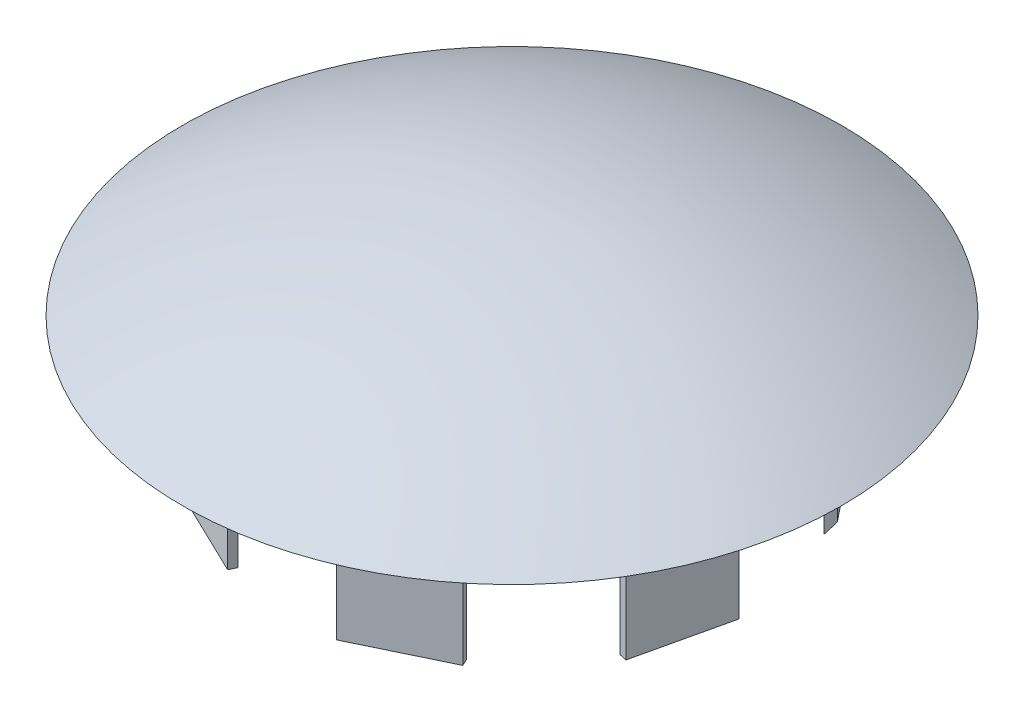
SolidWorks part; units mm, degrees
material "Custom Plastic PLA"
ref_plane "Front Plane" through (0, 0, 0) normal (0, 0, 1) x (1, 0, 0)
ref_plane "Top Plane" through (0, 0, 0) normal (0, 1, 0) x (1, 0, 0)
ref_plane "Right Plane" through (0, 0, 0) normal (1, 0, 0) x (0, 0, -1)
sketch "Sketch1" plane through (0, 0, 0) normal (0, 1, 0) x (1, 0, 0)
  line L6 (7.3408, 107.3746) -> (-14.4622, 96.8748)
  line L7 (-14.4622, 96.8748) -> (-29.5503, 77.9549)
  line L8 (-29.5503, 77.9549) -> (-34.9352, 54.3622)
  line L9 (-34.9352, 54.3622) -> (-29.5503, 30.7694)
  line L10 (-29.5503, 30.7694) -> (-14.4622, 11.8495)
  line L11 (-14.4622, 11.8495) -> (7.3408, 1.3497)
  line L12 (7.3408, 1.3497) -> (31.5403, 1.3497)
  line L13 (31.5403, 1.3497) -> (53.3433, 11.8495)
  line L14 (53.3433, 11.8495) -> (68.4314, 30.7694)
  line L15 (68.4314, 30.7694) -> (73.8163, 54.3622)
  line L16 (73.8163, 54.3622) -> (68.4314, 77.9549)
  line L17 (68.4314, 77.9549) -> (53.3433, 96.8748)
  line L18 (53.3433, 96.8748) -> (31.5403, 107.3746)
  line L31 (4.0802, 52.7357) -> (31.0802, 52.7357)
  line L32 (4.0802, 52.7357) -> (4.0802, 39.7357)
  line L33 (4.0802, 39.7357) -> (31.0802, 39.7357)
  line L34 (31.0802, 52.7357) -> (31.0802, 39.7357)
  line L35 (4.0802, 52.7357) -> (31.0802, 39.7357) construction
  line L36 (4.0802, 39.7357) -> (31.0802, 52.7357) construction
  line L61 (7.3408, 107.3746) -> (31.5403, 107.3746)
  line L62 (7.3408, 107.3746) -> (7.3408, 105.3746)
  line L63 (31.5403, 107.3746) -> (31.5403, 105.3746) construction
  line L65 (7.3408, 105.3746) -> (31.5403, 105.3746)
  line L66 (7.3408, 105.3746) -> (7.3408, 103.3746)
  line L67 (31.5403, 105.3746) -> (31.5403, 103.3746)
  line L68 (7.3408, 103.3746) -> (31.5403, 103.3746)
  line L69 (58.9964, 92.3606) -> (57.4327, 91.1136)
  line L70 (74.0845, 73.4407) -> (72.5208, 72.1937) construction
  line L71 (57.4327, 91.1136) -> (72.5208, 72.1937)
  line L72 (57.4327, 91.1136) -> (55.869, 89.8666)
  line L73 (55.869, 89.8666) -> (70.9572, 70.9467)
  line L74 (72.5208, 72.1937) -> (70.9572, 70.9467)
  line L75 (79.4647, 42.6136) -> (77.5148, 43.0587)
  line L76 (74.0798, 19.0209) -> (72.1299, 19.4659) construction
  line L77 (77.5148, 43.0587) -> (72.1299, 19.4659)
  line L78 (77.5148, 43.0587) -> (75.565, 43.5037)
  line L79 (75.565, 43.5037) -> (70.1801, 19.911)
  line L80 (72.1299, 19.4659) -> (70.1801, 19.911)
  line L81 (53.3327, -4.4059) -> (52.465, -2.6039)
  line L82 (31.5297, -14.9056) -> (30.662, -13.1037) construction
  line L83 (52.465, -2.6039) -> (30.662, -13.1037)
  line L84 (52.465, -2.6039) -> (51.5972, -0.802)
  line L85 (51.5972, -0.802) -> (29.7942, -11.3018)
  line L86 (30.662, -13.1037) -> (29.7942, -11.3018)
  line L87 (0.2784, -13.2913) -> (1.1461, -11.4893)
  line L88 (-21.5246, -2.7915) -> (-20.6568, -0.9896) construction
  line L89 (1.1461, -11.4893) -> (-20.6568, -0.9896)
  line L90 (1.1461, -11.4893) -> (2.0139, -9.6874)
  line L91 (2.0139, -9.6874) -> (-19.7891, 0.8123)
  line L92 (-20.6568, -0.9896) -> (-19.7891, 0.8123)
  line L93 (-39.7474, 22.6483) -> (-37.7975, 23.0934)
  line L94 (-45.1322, 46.2411) -> (-43.1824, 46.6861) construction
  line L95 (-37.7975, 23.0934) -> (-43.1824, 46.6861)
  line L96 (-37.7975, 23.0934) -> (-35.8476, 23.5384)
  line L97 (-35.8476, 23.5384) -> (-41.2325, 47.1311)
  line L98 (-43.1824, 46.6861) -> (-41.2325, 47.1311)
  line L99 (-36.6043, 76.3497) -> (-35.0406, 75.1027)
  line L100 (-21.5162, 95.2696) -> (-19.9525, 94.0226) construction
  line L101 (-35.0406, 75.1027) -> (-19.9525, 94.0226)
  line L102 (-35.0406, 75.1027) -> (-33.477, 73.8557)
  line L103 (-33.477, 73.8557) -> (-18.3888, 92.7756)
  line L104 (-19.9525, 94.0226) -> (-18.3888, 92.7756)
  circle A0 centre (17.5802, 46.2357) radius 61.0124 construction
  circle A1 centre (17.5802, 46.2357) radius 59.5269 construction
  circle A7 centre (17.5802, 46.2357) radius 82.9023
  point P6 (17.5802, 46.2357)
  point P46 (17.6415, 46.2663)
  point P67 (17.5802, 46.2357)
  dimension "D1" = 2
  dimension "D2" = 2
  dimension "D3" = 7
  dimension "D6" = 27
  dimension "D7" = 13
ref_plane "Plane1" through (0, 0, -46.2357) normal (0, 0, 1) x (1, 0, 0)
sketch "Sketch6" plane through (0, 0, -46.2357) normal (0, 0, 1) x (1, 0, 0)
  line L0 (16.2068, 19.7334) -> (16.2068, 24.2767)
  line L1 (16.2068, 24.2767) -> (100.5437, 0) construction
  line L2 (100.4824, 0) -> (-65.3221, 0) construction
  spline S0 degree 3 poles (100.5437, 0) (66.6377, 19.6839) (36.2957, 23.8771) (16.2068, 24.2767) knots 0 0 0 0 1 1 1 1
  spline S1 degree 3 poles (16.2068, 19.7334) (44.5503, 20.0467) (71.6583, 8.4773) (100.5437, 0) knots 0 0 0 0 1 1 1 1
  point P0 (16.2068, 19.7334)
revolve "Revolve3" add sketch "Sketch6" angle 360 about L0
extrude "Boss-Extrude1" add sketch "Sketch1" against normal blind 35 and the other way up to surface contours L104 L101 L102 L103 | L98 L95 L96 L97 | L92 L89 L90 L91 | L86 L83 L84 L85 | L80 L77 L78 L79 | L74 L71 L72 L73 | L66 L68 L67 L65
